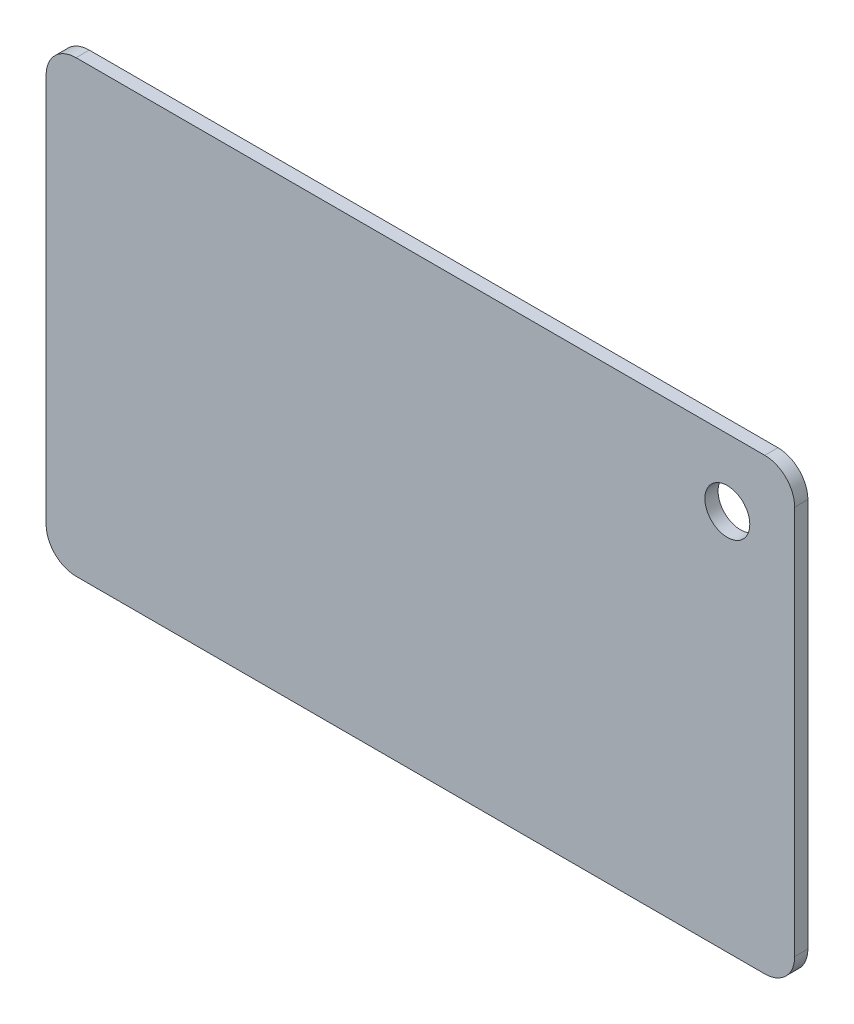
SolidWorks part; units mm, degrees
ref_plane "Front Plane" through (0, 0, 0) normal (0, 0, 1) x (1, 0, 0)
ref_plane "Top Plane" through (0, 0, 0) normal (0, 1, 0) x (1, 0, 0)
ref_plane "Right Plane" through (0, 0, 0) normal (1, 0, 0) x (0, 0, -1)
sketch "Sketch1" plane through (0, 0, 0) normal (0, 0, 1) x (1, 0, 0)
  line L1 (23, 15) -> (-23, 15)
  line L2 (25, 13) -> (25, -13)
  line L3 (23, -15) -> (-23, -15)
  line L4 (-25, 13) -> (-25, -13)
  line L5 (0, -15) -> (0, 15) construction
  line L6 (25, 0) -> (-25, 0) construction
  circle A0 centre (20.5, 10.5) radius 1.5
  arc A1 (23, 15) -> (25, 13) centre (23, 13) cw
  arc A2 (25, -13) -> (23, -15) centre (23, -13) cw
  arc A3 (-23, -15) -> (-25, -13) centre (-23, -13) cw
  arc A4 (-23, 15) -> (-25, 13) centre (-23, 13) ccw
  point P0 (0, 0)
  point P10 (25, -15)
  point P13 (-25, -15)
  point P16 (-25, 15)
  dimension "D3" = 3
  dimension "D6" = 2
  dimension "D1" = 50
  dimension "D2" = 30
  dimension "D4" = 4.5
  dimension "D5" = 4.5
extrude "Boss-Extrude1" add sketch "Sketch1" along normal blind 0.88
